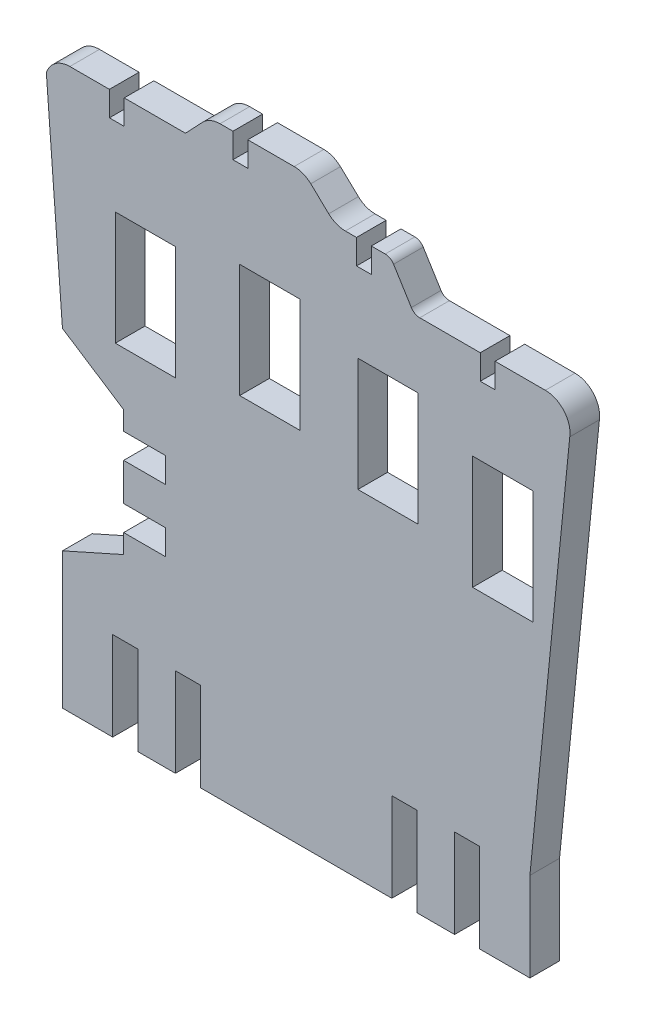
SolidWorks part; units mm, degrees
ref_plane "Front Plane" through (0, 0, 0) normal (0, 0, 1) x (1, 0, 0)
ref_plane "Top Plane" through (0, 0, 0) normal (0, 1, 0) x (1, 0, 0)
ref_plane "Right Plane" through (0, 0, 0) normal (1, 0, 0) x (0, 0, -1)
sketch "Sketch1" plane through (0, 0, 0) normal (0, 0, 1) x (1, 0, 0)
  line L3 (21.0774, 96.4872) -> (24.5143, 100.1188)
  line L5 (46.4328, 100.3093) -> (50.0643, 96.8725)
  line L35 (53.4283, 95.533) -> (55.6832, 95.533)
  line L40 (28.0688, 101.6488) -> (30.6832, 101.6488)
  line L41 (43.0688, 101.6488) -> (33.6832, 101.6488)
  line L45 (-2.3168, 96.4872) -> (5.6832, 96.4872)
  line L51 (83.7274, 87.8515) -> (83.7274, 82.8515)
  line L52 (83.7274, 82.8515) -> (80.7274, 82.8515)
  line L53 (80.7274, 82.8515) -> (80.7274, 87.8515)
  line L54 (55.6832, 95.533) -> (55.6832, 90.533)
  line L56 (21.0774, 96.4872) -> (8.6832, 96.4872)
  line L57 (58.6832, 95.533) -> (58.6832, 90.533)
  line L58 (58.6832, 90.533) -> (55.6832, 90.533)
  line L69 (33.6832, 101.6488) -> (33.6832, 96.6488)
  line L70 (33.6832, 96.6488) -> (30.6832, 96.6488)
  line L71 (30.6832, 96.6488) -> (30.6832, 101.6488)
  line L72 (8.6832, 96.4872) -> (8.6832, 91.4872)
  line L74 (5.6832, 91.4872) -> (5.6832, 96.4872)
  line L78 (8.6832, 91.4872) -> (5.6832, 91.4872)
  line L90 (83.7274, 87.8515) -> (93.8874, 87.8515)
  line L98 (91.3767, 68.9657) -> (79.1767, 68.9657)
  line L99 (91.3767, 68.9657) -> (91.3767, 45.9657)
  line L100 (91.3767, 45.9657) -> (79.1767, 45.9657)
  line L101 (79.1767, 68.9657) -> (79.1767, 45.9657)
  line L102 (68.1663, 74.5098) -> (55.9663, 74.5098)
  line L103 (68.1663, 74.5098) -> (68.1663, 51.5098)
  line L104 (68.1663, 51.5098) -> (55.9663, 51.5098)
  line L105 (55.9663, 74.5098) -> (55.9663, 51.5098)
  line L106 (44.2426, 79.0012) -> (32.0426, 79.0012)
  line L107 (44.2426, 79.0012) -> (44.2426, 56.0012)
  line L108 (44.2426, 56.0012) -> (32.0426, 56.0012)
  line L109 (32.0426, 79.0012) -> (32.0426, 56.0012)
  line L110 (19.0827, 75.5995) -> (6.8827, 75.5995)
  line L111 (19.0827, 75.5995) -> (19.0827, 52.5995)
  line L112 (19.0827, 52.5995) -> (6.8827, 52.5995)
  line L113 (6.8827, 75.5995) -> (6.8827, 52.5995)
  line L119 (98.839, 82.1578) -> (90.7717, 1.2791)
  line L120 (-7.0759, 93.0205) -> (-3.816, 49.8405)
  line L121 (8.5695, 41.7994) -> (-3.816, 49.8405)
  line L122 (8.5695, 41.7994) -> (8.5695, 37.9894)
  line L123 (8.5695, 37.9894) -> (17.0623, 37.9894)
  line L124 (75.5317, -16.6991) -> (67.9117, -16.6991)
  line L125 (-3.816, 10.8646) -> (-3.816, 1.2791)
  line L126 (58.6832, 95.533) -> (61.4893, 95.533)
  line L127 (63.1885, 94.5879) -> (66.7841, 88.7966)
  line L130 (68.4832, 87.8515) -> (80.7274, 87.8515)
  line L131 (8.5695, 32.9094) -> (17.0623, 32.9094)
  line L132 (17.0623, 37.9894) -> (17.0623, 32.9094)
  line L133 (8.5695, 25.3412) -> (17.0623, 25.3412)
  line L135 (8.5695, 20.2612) -> (17.0623, 20.2612)
  line L136 (17.0623, 25.3412) -> (17.0623, 20.2612)
  line L137 (8.5695, 16.3994) -> (-3.816, 10.8646)
  line L138 (8.5695, 32.9094) -> (8.5695, 25.3412)
  line L139 (8.5695, 20.2612) -> (8.5695, 16.3994)
  line L140 (90.7717, 1.2791) -> (90.7717, -16.6991)
  line L141 (90.7717, -16.6991) -> (80.6117, -16.6991)
  line L142 (-3.816, -16.6991) -> (-3.816, 1.2791)
  line L143 (62.8317, -16.6991) -> (24.124, -16.6991)
  line L145 (80.6117, -16.6991) -> (80.6117, 1.2791)
  line L146 (80.6117, 1.2791) -> (75.5317, 1.2791)
  line L147 (75.5317, -16.6991) -> (75.5317, 1.2791)
  line L149 (67.9117, -16.6991) -> (67.9117, 1.2791)
  line L150 (67.9117, 1.2791) -> (62.8317, 1.2791)
  line L151 (62.8317, -16.6991) -> (62.8317, 1.2791)
  line L153 (24.124, -16.6991) -> (24.124, 1.2791)
  line L154 (24.124, 1.2791) -> (19.044, 1.2791)
  line L155 (19.044, -16.6991) -> (19.044, 1.2791)
  line L157 (6.344, -16.6991) -> (6.344, 1.2791)
  line L158 (6.344, 1.2791) -> (11.424, 1.2791)
  line L159 (11.424, -16.6991) -> (11.424, 1.2791)
  line L160 (19.044, -16.6991) -> (11.424, -16.6991)
  line L161 (6.344, -16.6991) -> (-3.816, -16.6991)
  arc A5 (50.0643, 96.8725) -> (53.4283, 95.533) centre (53.4283, 100.427) ccw
  arc A6 (43.0688, 101.6488) -> (46.4328, 100.3093) centre (43.0688, 96.7548) cw
  arc A7 (24.5143, 100.1188) -> (28.0688, 101.6488) centre (28.0688, 96.7548) cw
  arc A12 (-2.3168, 96.4872) -> (-7.0759, 93.0205) centre (-2.3168, 91.4872) ccw
  arc A13 (93.8874, 87.8515) -> (98.839, 82.1578) centre (93.8874, 82.8515) cw
  arc A15 (66.7841, 88.7966) -> (68.4832, 87.8515) centre (68.4832, 89.8515) ccw
  arc A16 (61.4893, 95.533) -> (63.1885, 94.5879) centre (61.4893, 93.533) cw
  point P12 (-9.2732, 96.4872)
  point P18 (80.0035, 87.8515)
  dimension "D2" = 81.28
  dimension "D3" = 2
  dimension "D6" = 22
  dimension "D11" = 25.4
  dimension "D12" = 12.2
  dimension "D5" = 5
  dimension "D7" = 5
  dimension "D22" = 5.08
  dimension "D8" = 10.16
  dimension "D4" = 43.18
  dimension "D9" = 15
  dimension "D10" = 8
  dimension "D13" = 5
  dimension "D14" = 3
  dimension "D15" = 22
  dimension "D16" = 23
  dimension "D17" = 5
  dimension "D18" = 5
  dimension "D19" = 5.08
  dimension "D20" = 5.08
  dimension "D21" = 3.81
  dimension "D23" = 7.62
  dimension "D24" = 7.62
  dimension "D25" = 10.16
  dimension "D26" = 10.16
extrude "Boss-Extrude1" add sketch "Sketch1" along normal blind 6
